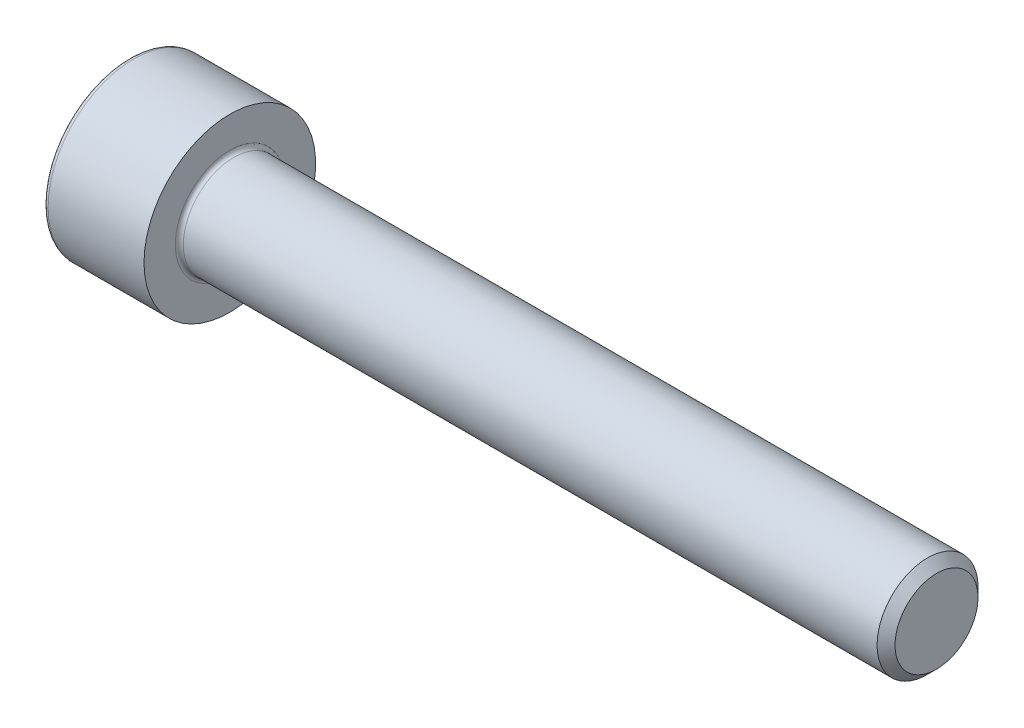
SolidWorks part; units mm, degrees
ref_plane "Plane1" through (0, 0, 0) normal (0, 0, 1) x (1, 0, 0)
ref_plane "Plane2" through (0, 0, 0) normal (0, 1, 0) x (1, 0, 0)
ref_plane "Plane3" through (0, 0, 0) normal (1, 0, 0) x (0, 0, -1)
sketch "BodySke" plane through (0, 0, 0) normal (0, 0, 1) x (1, 0, 0)
  line L0 (0, 0) -> (0, 4.25)
  line L1 (0, 4.25) -> (5, 4.25)
  line L2 (5, 4.25) -> (5, 2.5)
  line L3 (5, 2.5) -> (39.555, 2.5)
  line L4 (40, 2.055) -> (40, 0)
  line L5 (40, 0) -> (0, 0)
  line L6 (-31.75, 0) -> (127, 0) construction
  line L8 (40, 2.055) -> (39.555, 2.5)
  line L10 (40, -2.055) -> (39.555, -2.5) construction
  line L11 (4.2, 9.525) -> (4.2, 3.175) construction
  line L12 (5, 9.525) -> (5, 3.175) construction
  line L13 (-5, 9.525) -> (-5, 3.175) construction
  dimension "Head_ht" = 5
  dimension "Length" = 35
  dimension "Body_ch_ang" = 45
  dimension "Diameter" = 5
  dimension "Minor_dia" = 4.11
  dimension "Advance" = 0.8
  dimension "Thread_nom" = 35
  dimension "Thread_length" = 45
  dimension "Head_dia" = 8.5
revolve "Base-Revolve" add sketch "BodySke" angle 360 about L6
cosmetic thread "ThreadCosmetic" parameters "Thread_length"=32.6, "Thread_minor"=4.11
fillet "Fillet1" radius 0.2 1 edges at (5, 0, 2.5)
fillet "Fillet2" radius 0.25 1 edges at (0, 0, 4.25)
sketch "Sketch2" plane through (0, 0, 0) normal (0, 0, 1) x (1, 0, 0)
  line L0 (0, 2.042) -> (2.5, 2.042)
  line L1 (2.5, 2.042) -> (3.6789, 0)
  line L2 (-31.75, 0) -> (127, 0) construction
  line L3 (3.6789, 0) -> (0, 0)
  line L4 (0, 0) -> (0, 2.042)
  line L6 (0, 0) -> (47.625, 0) construction
  dimension "D1" = 2.042
  dimension "D2" = 60
  dimension "Depth" = 2.5
revolve "Hex-PreBroach" cut sketch "Sketch2" angle 360 about L6
sketch "Sketch3" plane through (0, 0, 0) normal (-1, 0, 0) x (0, 0.5, 0.866)
  line L0 (1.1789, 2.042) -> (-1.1789, 2.042)
  line L1 (-1.1789, 2.042) -> (-2.3579, 0)
  line L2 (1.1789, 2.042) -> (2.3579, 0)
  line L3 (1.1789, -2.042) -> (2.3579, 0)
  line L4 (1.1789, -2.042) -> (-1.1789, -2.042)
  line L5 (-1.1789, -2.042) -> (-2.3579, 0)
  dimension "D1" = 2.042
  dimension "D2" = 2.042
  dimension "Hex_size" = 4.084
extrude "Hex" cut sketch "Sketch3" against normal blind 2.5
sketch "ThdSchSke" plane through (0, 0, 0) normal (0, 0, 1) x (1, 0, 0)
  line L0 (7.4, -2.055) -> (7.0884, -2.5)
  line L1 (7.4, -2.055) -> (7.7116, -2.5)
  line L2 (7.7116, -2.5) -> (7.7116, -3.125)
  line L3 (-3.175, 0) -> (5.1513, 0) construction
  line L4 (0, 4) -> (0, -4) construction
  line L5 (7.7116, -3.125) -> (7.0884, -3.125)
  line L6 (7.0884, -3.125) -> (7.0884, -2.5)
  dimension "Thread_minor" = 4.11
  dimension "Diameter" = 5
  dimension "SideAngle" = 55
  dimension "VeeAngle" = 70
  dimension "Overcut" = 6.25
  dimension "Start" = 7.4
revolve "ThreadSchematic" [suppressed] cut sketch "ThdSchSke" angle 360 about L3
pattern_linear "ThdSchPat" [suppressed]
equation "\"D2@Sketch3\" = \"Hex_size@Sketch3\" / 2"
equation "\"D1@Sketch3\" = \"Hex_size@Sketch3\" / 2"
equation "\"D1@Sketch2\" = \"Hex_size@Sketch3\" / 2"
equation "\"Thread_minor@ThreadCosmetic\"  =  \"Minor_dia@BodySke\""
equation "\"Depth@Sketch2\" =  \"Key_eng@Hex\""
equation "\"Thread_length@ThreadCosmetic\" = ((sgn( (\"Length@BodySke\" - \"Advance@BodySke\" * 3.0) - \"Thread_nom@BodySke\" )-1)*( (\"Length@BodySke\" - \"Advance@BodySke\" * 3.0) - \"Thread_nom@BodySke\" ))/-2+ \"Thread_nom@BodySke\""
equation "\"Thread_minor@ThdSchSke\" = \"Minor_dia@BodySke\""
equation "\"Diameter@ThdSchSke\" = \"Diameter@BodySke\""
equation "\"Overcut@ThdSchSke\" = \"Diameter@BodySke\" * 1.25"
equation "\"Start@ThdSchSke\" = \"Head_ht@BodySke\" + \"Length@BodySke\" - \"Thread_length@ThreadCosmetic\"  '---Non-countersunk---"
equation "\"Num_threads@ThdSchPat\" = int( \"Thread_length@ThreadCosmetic\" / \"Advance@BodySke\" + 0.999 )  + 1"
equation "\"Advance@ThdSchPat\" = \"Thread_length@ThreadCosmetic\" /  (\"Num_threads@ThdSchPat\" - 1) 'relax it"
equation "\"Num_threads@ThdSchPat\" = \"Num_threads@ThdSchPat\" - sgn( \"Num_threads@ThdSchPat\" - 1) '---chamfered tips only---"
